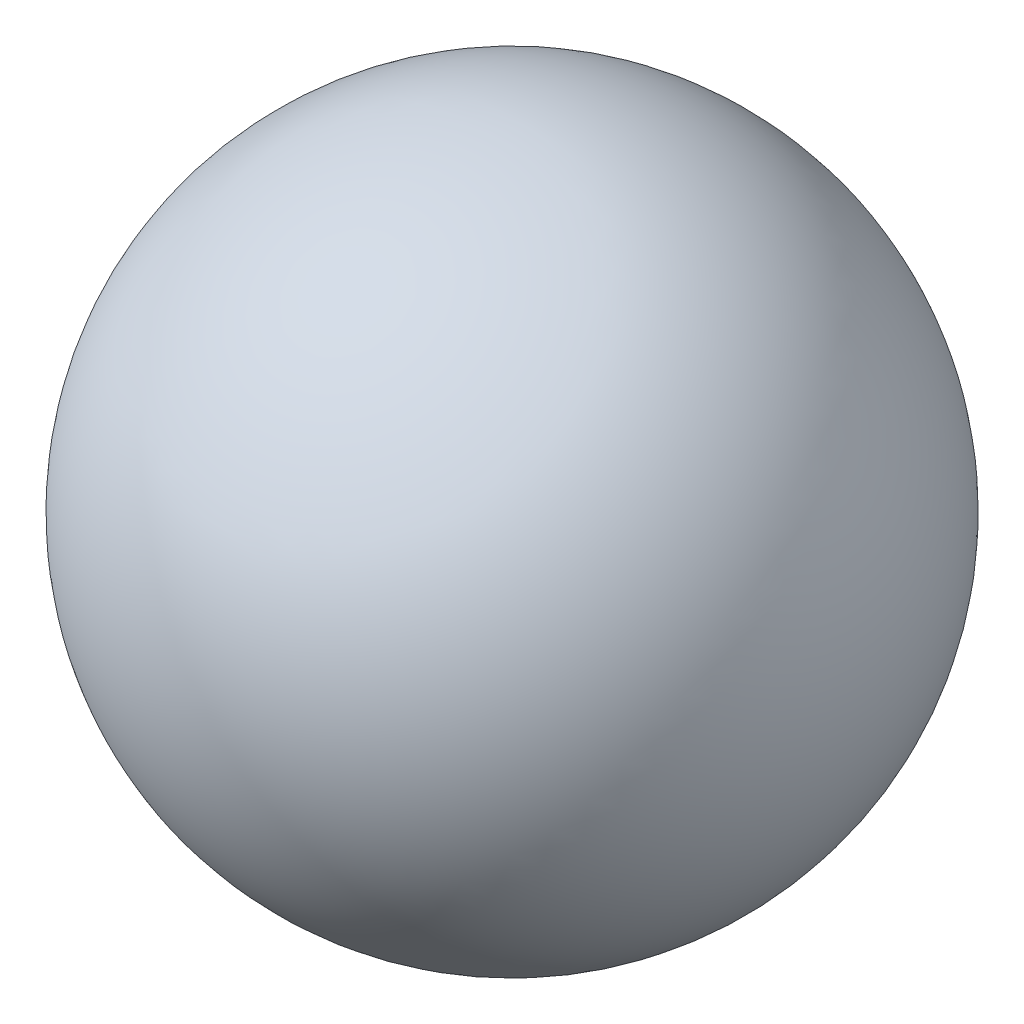
SolidWorks part; units mm, degrees
ref_plane "Front Plane" through (0, 0, 0) normal (0, 0, 1) x (1, 0, 0)
ref_plane "Horizon" through (0, 0, 0) normal (0, 1, 0) x (1, 0, 0)
ref_plane "0deg" through (0, 0, 0) normal (1, 0, 0) x (0, 0, -1)
sketch "Sketch1" plane through (0, 0, 0) normal (0, 1, 0) x (1, 0, 0)
  line L0 (0, -44.45) -> (0, 44.45)
  arc A0 (0, 42.45) -> (0, -42.45) centre (0, 0) ccw
  arc A1 (0, 44.45) -> (0, -44.45) centre (0, 0) ccw
  point P7 (0, 0)
  dimension "D1" = 88.9
  dimension "D2" = 2
revolve "Revolve1" add sketch "Sketch1" angle 360 about L0
sketch "Heading" plane through (0, 0, 0) normal (0, 1, 0) x (1, 0, 0)
  line L0 (0, 0) -> (0, -44.45)
  line L1 (0, 0) -> (-22.225, -38.4948) construction
  line L2 (0, 0) -> (-38.4948, -22.225) construction
  line L3 (0, 0) -> (-44.45, 0) construction
  line L4 (0, 0) -> (-38.4948, 22.225) construction
  line L5 (0, 0) -> (-22.225, 38.4948) construction
  line L6 (0, 0) -> (0, 44.45) construction
  line L7 (0, 0) -> (22.225, 38.4948) construction
  line L8 (0, 0) -> (38.4948, 22.225) construction
  line L9 (0, 0) -> (44.45, 0) construction
  line L10 (0, 0) -> (38.4948, -22.225) construction
  line L11 (0, 0) -> (22.225, -38.4948) construction
  line L12 (0, 0) -> (0, -44.45) construction
  line L13 (0, 0) -> (-22.225, -38.4948) construction
  circle A0 centre (0, 0) radius 44.45 construction
  dimension "D1" = 88.9
  dimension "D3" = 30
  dimension "D2" = 12
sketch "Pitch" plane through (0, 0, 0) normal (1, 0, 0) x (0, 0, -1)
  line L0 (0, 0) -> (38.4948, 22.225) construction
  line L1 (0, 0) -> (22.225, 38.4948) construction
  line L2 (0, 0) -> (0, 44.45) construction
  line L3 (0, 0) -> (-22.225, 38.4948) construction
  line L4 (0, 0) -> (-38.4948, 22.225) construction
  line L5 (0, 0) -> (-44.45, 0) construction
  line L6 (0, 0) -> (-38.4948, -22.225) construction
  line L7 (0, 0) -> (-22.225, -38.4948) construction
  line L8 (0, 0) -> (0, -44.45) construction
  line L9 (0, 0) -> (22.225, -38.4948) construction
  line L10 (0, 0) -> (38.4948, -22.225) construction
  line L11 (0, 0) -> (38.4948, 22.225) construction
  line L12 (0, 0) -> (22.225, 38.4948) construction
  circle A0 centre (0, 0) radius 44.45 construction
  dimension "D1" = 88.9
  dimension "D3" = 30
  dimension "D2" = 11
ref_plane "Hdg3" through (0, 0, 0) normal (-0.866, 0, 0.5) x (0.5, 0, 0.866)
ref_plane "Hdg6" through (0, 0, 0) normal (-0.5, 0, 0.866) x (0.866, 0, 0.5)
ref_plane "Hdg9" through (0, 0, 0) normal (0, 0, 1) x (1, 0, 0)
ref_plane "Hdg12" through (0, 0, 0) normal (0.5, 0, 0.866) x (0.866, 0, -0.5)
ref_plane "Hdg15" through (0, 0, 0) normal (0.866, 0, 0.5) x (0.5, 0, -0.866)
ref_plane "Hdg18" through (0, 0, 0) normal (1, 0, 0) x (0, 0, -1)
ref_plane "Hdg21" through (0, 0, 0) normal (0.866, 0, -0.5) x (-0.5, 0, -0.866)
ref_plane "Hdg24" through (0, 0, 0) normal (0.5, 0, -0.866) x (-0.866, 0, -0.5)
ref_plane "Hdg27" through (0, 0, 0) normal (0, 0, -1) x (-1, 0, 0)
ref_plane "Hdg30" through (0, 0, 0) normal (-0.5, 0, -0.866) x (-0.866, 0, 0.5)
ref_plane "Hdg33" through (0, 0, 0) normal (-0.866, 0, -0.5) x (-0.5, 0, 0.866)
ref_plane "Hdg0" through (0, 0, 0) normal (-1, 0, 0) x (0, 0, 1)
sketch "Sketch2" plane through (0, 0, 0) normal (-0.866, 0, 0.5) x (0.5, 0, 0.866)
  line L0 (0, 0) -> (38.4948, 22.225) construction
  line L1 (0, 0) -> (22.225, 38.4948) construction
  line L2 (0, 0) -> (0, 44.45) construction
  line L3 (0, 0) -> (-22.225, 38.4948) construction
  line L4 (0, 0) -> (-38.4948, 22.225) construction
  line L5 (0, 0) -> (-44.45, 0) construction
  line L6 (0, 0) -> (-38.4948, -22.225) construction
  line L7 (0, 0) -> (-22.225, -38.4948) construction
  line L8 (0, 0) -> (0, -44.45) construction
  line L9 (0, 0) -> (22.225, -38.4948) construction
  line L10 (0, 0) -> (38.4948, -22.225) construction
  line L11 (0, 0) -> (38.4948, 22.225) construction
  line L12 (0, 0) -> (22.225, 38.4948) construction
  circle A0 centre (0, 0) radius 44.45 construction
  dimension "D1" = 88.9
  dimension "D3" = 30
  dimension "D2" = 11
sketch "Sketch3" plane through (0, 0, 0) normal (-0.5, 0, 0.866) x (0.866, 0, 0.5)
  line L0 (0, 0) -> (38.4948, 22.225) construction
  line L1 (0, 0) -> (22.225, 38.4948) construction
  line L2 (0, 0) -> (0, 44.45) construction
  line L3 (0, 0) -> (-22.225, 38.4948) construction
  line L4 (0, 0) -> (-38.4948, 22.225) construction
  line L5 (0, 0) -> (-44.45, 0) construction
  line L6 (0, 0) -> (-38.4948, -22.225) construction
  line L7 (0, 0) -> (-22.225, -38.4948) construction
  line L8 (0, 0) -> (0, -44.45) construction
  line L9 (0, 0) -> (22.225, -38.4948) construction
  line L10 (0, 0) -> (38.4948, -22.225) construction
  line L11 (0, 0) -> (38.4948, 22.225) construction
  line L12 (0, 0) -> (22.225, 38.4948) construction
  circle A0 centre (0, 0) radius 44.45 construction
  dimension "D1" = 88.9
  dimension "D3" = 30
  dimension "D2" = 11
sketch "Sketch4" plane through (0, 0, 0) normal (0, 0, 1) x (1, 0, 0)
  line L0 (0, 0) -> (38.4948, 22.225) construction
  line L1 (0, 0) -> (22.225, 38.4948) construction
  line L2 (0, 0) -> (0, 44.45) construction
  line L3 (0, 0) -> (-22.225, 38.4948) construction
  line L4 (0, 0) -> (-38.4948, 22.225) construction
  line L5 (0, 0) -> (-44.45, 0) construction
  line L6 (0, 0) -> (-38.4948, -22.225) construction
  line L7 (0, 0) -> (-22.225, -38.4948) construction
  line L8 (0, 0) -> (0, -44.45) construction
  line L9 (0, 0) -> (22.225, -38.4948) construction
  line L10 (0, 0) -> (38.4948, -22.225) construction
  line L11 (0, 0) -> (38.4948, 22.225) construction
  line L12 (0, 0) -> (22.225, 38.4948) construction
  circle A0 centre (0, 0) radius 44.45 construction
  dimension "D1" = 88.9
  dimension "D3" = 30
  dimension "D2" = 11
sketch "Sketch5" plane through (0, 0, 0) normal (0.5, 0, 0.866) x (0.866, 0, -0.5)
  line L0 (0, 0) -> (38.4948, 22.225) construction
  line L1 (0, 0) -> (22.225, 38.4948) construction
  line L2 (0, 0) -> (0, 44.45) construction
  line L3 (0, 0) -> (-22.225, 38.4948) construction
  line L4 (0, 0) -> (-38.4948, 22.225) construction
  line L5 (0, 0) -> (-44.45, 0) construction
  line L6 (0, 0) -> (-38.4948, -22.225) construction
  line L7 (0, 0) -> (-22.225, -38.4948) construction
  line L8 (0, 0) -> (0, -44.45) construction
  line L9 (0, 0) -> (22.225, -38.4948) construction
  line L10 (0, 0) -> (38.4948, -22.225) construction
  line L11 (0, 0) -> (38.4948, 22.225) construction
  line L12 (0, 0) -> (22.225, 38.4948) construction
  circle A0 centre (0, 0) radius 44.45 construction
  dimension "D1" = 88.9
  dimension "D3" = 30
  dimension "D2" = 11
sketch "Sketch6" plane through (0, 0, 0) normal (0.866, 0, 0.5) x (0.5, 0, -0.866)
  line L0 (0, 0) -> (38.4948, 22.225) construction
  line L1 (0, 0) -> (22.225, 38.4948) construction
  line L2 (0, 0) -> (0, 44.45) construction
  line L3 (0, 0) -> (-22.225, 38.4948) construction
  line L4 (0, 0) -> (-38.4948, 22.225) construction
  line L5 (0, 0) -> (-44.45, 0) construction
  line L6 (0, 0) -> (-38.4948, -22.225) construction
  line L7 (0, 0) -> (-22.225, -38.4948) construction
  line L8 (0, 0) -> (0, -44.45) construction
  line L9 (0, 0) -> (22.225, -38.4948) construction
  line L10 (0, 0) -> (38.4948, -22.225) construction
  line L11 (0, 0) -> (38.4948, 22.225) construction
  line L12 (0, 0) -> (22.225, 38.4948) construction
  circle A0 centre (0, 0) radius 44.45 construction
  dimension "D1" = 88.9
  dimension "D3" = 30
  dimension "D2" = 11
